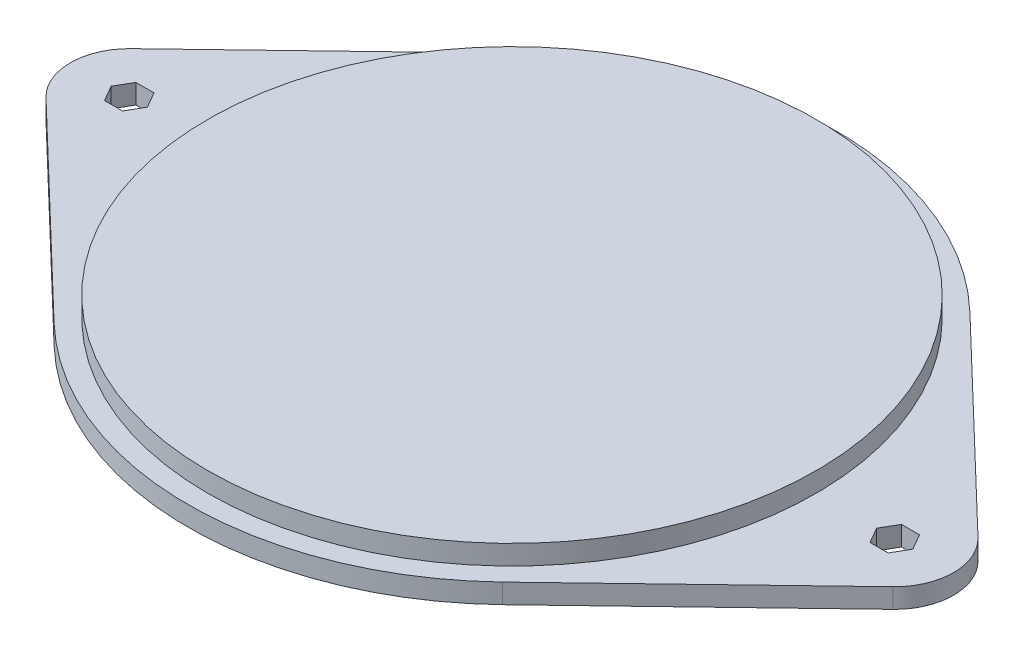
SolidWorks part; units mm, degrees
ref_plane "Front" through (0, 0, 0) normal (0, 0, 1) x (1, 0, 0)
ref_plane "Top" through (0, 0, 0) normal (0, 1, 0) x (1, 0, 0)
ref_plane "Right" through (0, 0, 0) normal (1, 0, 0) x (0, 0, -1)
sketch "Sketch1" plane through (0, 0, 0) normal (0, 1, 0) x (1, 0, 0)
  line L0 (57.1154, 59.5322) -> (107.8846, 10.824)
  line L1 (107.8846, -10.824) -> (57.1154, -59.5322)
  line L2 (0, -50) -> (0, 50) construction
  line L3 (-107.8846, -10.824) -> (-57.1154, -59.5322)
  line L4 (-57.1154, 59.5322) -> (-107.8846, 10.824)
  circle A0 centre (0, 0) radius 82.5
  circle A2 centre (97.5, 0) radius 15
  circle A3 centre (-97.5, 0) radius 15
  dimension "D1" = 165
  dimension "D2" = 30
  dimension "D3" = 97.5
extrude "Boss-Extrude1" add sketch "Sketch1" along normal blind 5 contours L4 A3 L3 A0 | A3 | A2 L0 A0 L1 | A2 | A0 A3 L3 | A2 A0 L1
sketch "Sketch2" plane through (0, 5, 0) normal (0, 1, 0) x (1, 0, 0)
  circle A0 centre (0, 0) radius 77.5
  dimension "D1" = 155
extrude "Boss-Extrude2" add sketch "Sketch2" along normal blind 5
sketch "Sketch3" plane through (0, 5, 0) normal (0, 1, 0) x (1, 0, 0)
  line L1 (-95.1906, 4) -> (-99.8094, 4)
  line L2 (-99.8094, 4) -> (-102.1188, 0)
  line L3 (-102.1188, 0) -> (-99.8094, -4)
  line L4 (-99.8094, -4) -> (-95.1906, -4)
  line L5 (-95.1906, -4) -> (-92.8812, 0)
  line L6 (-92.8812, 0) -> (-95.1906, 4)
  line L7 (99.8094, 4) -> (95.1906, 4)
  line L8 (95.1906, 4) -> (92.8812, 0)
  line L9 (92.8812, 0) -> (95.1906, -4)
  line L10 (95.1906, -4) -> (99.8094, -4)
  line L11 (99.8094, -4) -> (102.1188, 0)
  line L12 (102.1188, 0) -> (99.8094, 4)
  circle A8 centre (-97.5, 0) radius 4 construction
  arc A9 (-107.8846, 10.824) -> (-107.8846, -10.824) centre (-97.5, 0) ccw construction
  circle A10 centre (97.5, 0) radius 4 construction
  arc A11 (107.8846, -10.824) -> (107.8846, 10.824) centre (97.5, 0) ccw construction
  dimension "D1" = 8
extrude "Cut-Extrude1" cut sketch "Sketch3" against normal through all
equation "\"Kova_d\"= 155mm"
equation "\"Kova_h\"= 100mm"
equation "\"Plaka_h\"= 200mm"
equation "\"Plaka_L\"= 250mm"
equation "\"Saplama_d\"= 5mm"
equation "\"D1@Sketch1\"=\"Kova_d\"+10"
equation "\"D3@Sketch1\"=\"Kova_d\"/2+20"
equation "\"D1@Sketch2\"=\"Kova_d\""
